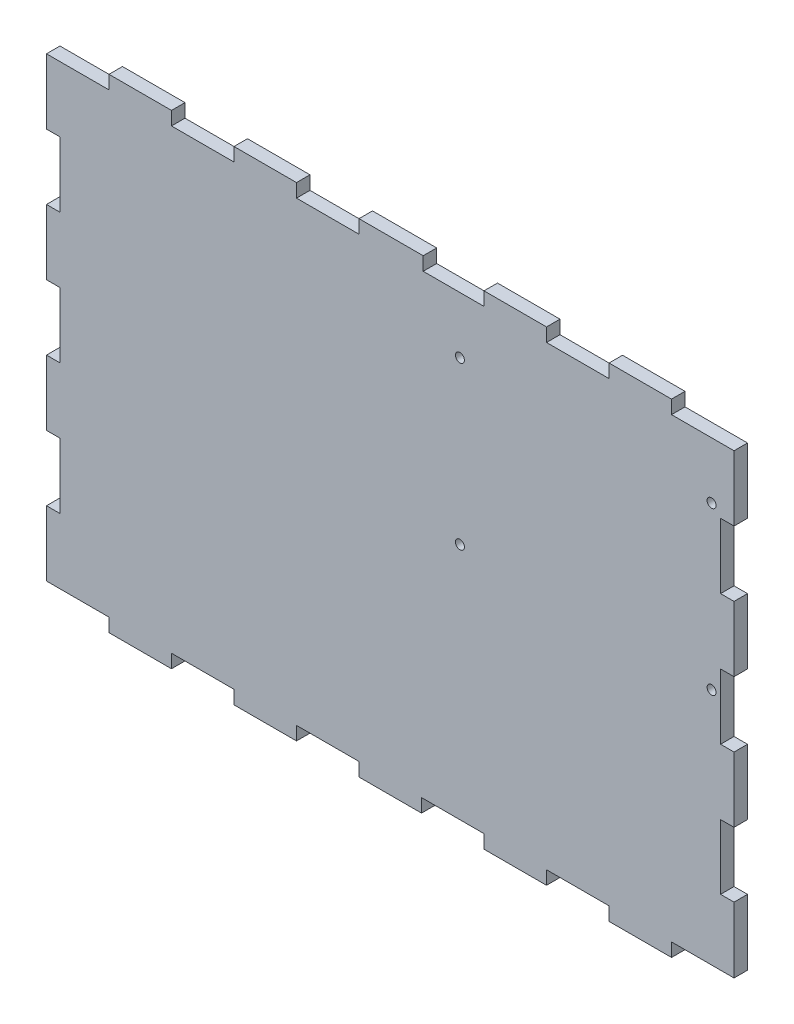
SolidWorks part; units mm, degrees
ref_plane "Alzado" through (0, 0, 0) normal (0, 0, 1) x (1, 0, 0)
ref_plane "Planta" through (0, 0, 0) normal (0, 1, 0) x (1, 0, 0)
ref_plane "Vista lateral" through (0, 0, 0) normal (1, 0, 0) x (0, 0, -1)
sketch "Croquis1" plane through (0, 0, 0) normal (0, 0, 1) x (1, 0, 0)
  line L0 (0, -17.0016) -> (0, -14.0016)
  line L1 (-48.0137, -14.0016) -> (0.3763, -14.0016) construction
  line L2 (0, -17.0016) -> (104.61, -17.0016)
  line L3 (101.61, -17.0016) -> (101.61, -49.332) construction
  line L4 (-227.5797, -78.0016) -> (94.1343, -78.0016) construction
  line L5 (-48.39, -14.0016) -> (-48.39, -78.0016) construction
  line L6 (78.6222, -39.0016) -> (-38.712, -39.0016) construction
  line L7 (0, -14.0016) -> (0, -17.0016) construction
  line L8 (0.3763, -17.0016) -> (-48.0137, -17.0016) construction
  line L9 (-48.39, -14.0016) -> (-38.712, -14.0016)
  line L10 (-38.712, -14.0016) -> (-38.712, -17.0016)
  line L11 (-38.712, -17.0016) -> (-29.034, -17.0016)
  line L12 (-29.034, -17.0016) -> (-29.034, -14.0016)
  line L13 (-29.034, -14.0016) -> (-19.356, -14.0016)
  line L14 (-19.356, -14.0016) -> (-19.356, -17.0016)
  line L15 (-19.356, -17.0016) -> (-9.678, -17.0016)
  line L16 (-9.678, -17.0016) -> (-9.678, -14.0016)
  line L17 (-9.678, -14.0016) -> (0, -14.0016)
  line L18 (104.61, -17.0016) -> (104.61, -78.0016) construction
  line L19 (104.61, -17.0016) -> (104.61, -29.2016)
  line L20 (104.61, -29.2016) -> (101.61, -29.2016)
  line L21 (101.61, -29.2016) -> (101.61, -41.4016)
  line L22 (101.61, -41.4016) -> (104.61, -41.4016)
  line L23 (104.61, -41.4016) -> (104.61, -53.6016)
  line L24 (104.61, -53.6016) -> (101.61, -53.6016)
  line L25 (101.61, -53.6016) -> (101.61, -65.8016)
  line L26 (101.61, -65.8016) -> (104.61, -65.8016)
  line L27 (104.61, -65.8016) -> (104.61, -78.0016)
  line L28 (-45.39, -56.5563) -> (-45.39, 45.6638) construction
  line L29 (-48.39, -14.0016) -> (-48.39, -26.8016)
  line L30 (-48.39, -26.8016) -> (-45.39, -26.8016)
  line L31 (-45.39, -26.8016) -> (-45.39, -39.6016)
  line L32 (-45.39, -39.6016) -> (-48.39, -39.6016)
  line L33 (-48.39, -39.6016) -> (-48.39, -52.4016)
  line L34 (-48.39, -52.4016) -> (-45.39, -52.4016)
  line L35 (-45.39, -52.4016) -> (-45.39, -65.2016)
  line L36 (-45.39, -65.2016) -> (-48.39, -65.2016)
  line L37 (-48.39, -65.2016) -> (-48.39, -78.0016)
  line L38 (-102.1267, -75.0016) -> (76.3072, -75.0016) construction
  line L39 (-124.0097, -156.1001) -> (179.5642, -156.1001) construction
  line L40 (-48.0137, -153.1001) -> (104.9863, -153.1001) construction
  line L41 (-48.39, -78.0016) -> (-34.4809, -78.0016)
  line L42 (-34.4809, -78.0016) -> (-34.4809, -75.0016)
  line L43 (-34.4809, -75.0016) -> (-20.5718, -75.0016)
  line L44 (-20.5718, -75.0016) -> (-20.5718, -78.0016)
  line L45 (-20.5718, -78.0016) -> (-6.6627, -78.0016)
  line L46 (-6.6627, -78.0016) -> (-6.6627, -75.0016)
  line L47 (-6.6627, -75.0016) -> (7.2464, -75.0016)
  line L48 (7.2464, -75.0016) -> (7.2464, -78.0016)
  line L49 (7.2464, -78.0016) -> (21.1555, -78.0016)
  line L50 (21.1555, -78.0016) -> (21.1555, -75.0016)
  line L51 (21.1555, -75.0016) -> (35.0645, -75.0016)
  line L52 (35.0645, -75.0016) -> (35.0645, -78.0016)
  line L53 (35.0645, -78.0016) -> (48.9736, -78.0016)
  line L54 (48.9736, -78.0016) -> (48.9736, -75.0016)
  line L55 (48.9736, -75.0016) -> (62.8827, -75.0016)
  line L56 (62.8827, -75.0016) -> (62.8827, -78.0016)
  line L57 (62.8827, -78.0016) -> (76.7918, -78.0016)
  line L58 (76.7918, -78.0016) -> (76.7918, -75.0016)
  line L59 (76.7918, -75.0016) -> (90.7009, -75.0016)
  line L60 (90.7009, -75.0016) -> (90.7009, -78.0016)
  line L61 (90.7009, -78.0016) -> (104.61, -78.0016)
  line L62 (-48.39, -153.1001) -> (-48.39, -260.7101) construction
  line L63 (-48.0137, -260.7101) -> (104.9863, -260.7101) construction
  line L64 (104.61, -153.1001) -> (104.61, -260.7101) construction
  line L65 (-68.3871, -257.7101) -> (145.2495, -257.7101) construction
  line L66 (101.61, -78.0016) -> (101.61, -269.1968) construction
  line L67 (-45.39, -153.1001) -> (-45.39, -251.8965) construction
  line L68 (-34.4809, -78.0016) -> (-34.4809, -243.0877) construction
  line L69 (-20.5718, -78.0016) -> (-20.5718, -243.0877) construction
  line L70 (-6.6627, -75.0016) -> (-6.6627, -243.0877) construction
  line L71 (7.2464, -75.0016) -> (7.2464, -243.0877) construction
  line L72 (21.1555, -75.0016) -> (21.1555, -243.0877) construction
  line L73 (35.0645, -75.0016) -> (35.0645, -243.0877) construction
  line L74 (48.9736, -75.0016) -> (48.9736, -243.0877) construction
  line L75 (62.8827, -75.0016) -> (62.8827, -243.0877) construction
  line L76 (76.7918, -75.0016) -> (76.7918, -243.0877) construction
  line L77 (90.7009, -75.0016) -> (90.7009, -243.0877) construction
  line L78 (-34.4809, -156.1001) -> (-48.39, -156.1001)
  line L79 (-34.4809, -156.1001) -> (-34.4809, -153.1001)
  line L80 (-34.4809, -153.1001) -> (-20.5718, -153.1001)
  line L81 (-20.5718, -153.1001) -> (-20.5718, -156.1001)
  line L82 (-20.5718, -156.1001) -> (-6.6627, -156.1001)
  line L83 (-6.6627, -156.1001) -> (-6.6627, -153.1001)
  line L84 (-6.6627, -153.1001) -> (7.2464, -153.1001)
  line L85 (7.2464, -153.1001) -> (7.2464, -156.1001)
  line L86 (7.2464, -156.1001) -> (21.1555, -156.1001)
  line L87 (21.1555, -156.1001) -> (21.1555, -153.1001)
  line L88 (21.1555, -153.1001) -> (35.4409, -153.1001)
  line L89 (35.4409, -153.1001) -> (35.4409, -156.1001)
  line L90 (35.4409, -156.1001) -> (48.9736, -156.1001)
  line L91 (48.9736, -156.1001) -> (48.9736, -153.1001)
  line L92 (48.9736, -153.1001) -> (62.8827, -153.1001)
  line L93 (62.8827, -153.1001) -> (62.8827, -156.1001)
  line L94 (62.8827, -156.1001) -> (76.7918, -156.1001)
  line L95 (76.7918, -156.1001) -> (76.7918, -153.1001)
  line L96 (76.7918, -153.1001) -> (90.7009, -153.1001)
  line L97 (90.7009, -153.1001) -> (90.7009, -156.1001)
  line L98 (90.7009, -156.1001) -> (104.61, -156.1001)
  line L99 (-48.39, -257.7101) -> (-34.4809, -257.7101)
  line L100 (-34.4809, -257.7101) -> (-34.4809, -260.7101)
  line L101 (-34.4809, -260.7101) -> (-20.5718, -260.7101)
  line L102 (-20.5718, -260.7101) -> (-20.5718, -257.7101)
  line L103 (-20.5718, -257.7101) -> (-6.6627, -257.7101)
  line L104 (-6.6627, -257.7101) -> (-6.6627, -260.7101)
  line L105 (-6.6627, -260.7101) -> (7.2464, -260.7101)
  line L106 (7.2464, -260.7101) -> (7.2464, -257.7101)
  line L107 (7.2464, -257.7101) -> (21.1555, -257.7101)
  line L108 (21.1555, -257.7101) -> (21.1555, -260.7101)
  line L109 (21.1555, -260.7101) -> (35.0645, -260.7101)
  line L110 (35.0645, -260.7101) -> (35.0645, -257.7101)
  line L111 (35.0645, -257.7101) -> (48.9736, -257.7101)
  line L112 (48.9736, -257.7101) -> (48.9736, -260.7101)
  line L113 (48.9736, -260.7101) -> (62.8827, -260.7101)
  line L114 (62.8827, -260.7101) -> (62.8827, -257.7101)
  line L115 (62.8827, -257.7101) -> (76.7918, -257.7101)
  line L116 (76.7918, -257.7101) -> (76.7918, -260.7101)
  line L117 (76.7918, -260.7101) -> (90.7009, -260.7101)
  line L118 (90.7009, -260.7101) -> (90.7009, -257.7101)
  line L119 (90.7009, -257.7101) -> (104.61, -257.7101)
  line L120 (-225.8763, -14.0016) -> (-225.8763, -78.0016) construction
  line L121 (-289.8763, -78.0016) -> (-225.8763, -78.0016) construction
  line L122 (-225.8763, -78.0016) -> (-225.8763, -287.7111) construction
  line L123 (-289.8763, -78.0016) -> (-289.8763, -287.7111) construction
  line L124 (-289.8763, -287.7111) -> (-225.8763, -287.7111) construction
  line L125 (-48.0137, -26.8016) -> (-105.1743, -26.8016) construction
  line L126 (-48.0137, -39.6016) -> (-94.3752, -39.6016) construction
  line L127 (-48.0137, -52.4016) -> (-71.4298, -52.4016) construction
  line L128 (-48.0137, -65.2016) -> (-67.3697, -65.2016) construction
  line L129 (-277.0763, -73.8444) -> (-277.0763, -111.8004) construction
  line L130 (-264.2763, -73.8444) -> (-264.2763, -111.8004) construction
  line L131 (-251.4763, -90.832) -> (-251.4763, -128.788) construction
  line L132 (-238.6763, -73.8444) -> (-238.6763, -111.8004) construction
  line L133 (-228.8763, -73.8444) -> (-228.8763, -93.389) construction
  line L134 (165.7334, -156.1001) -> (174.9334, -156.1001)
  line L135 (174.9334, -156.1001) -> (174.9334, -153.1001)
  line L136 (174.9334, -153.1001) -> (187.1334, -153.1001)
  line L137 (187.1334, -153.1001) -> (187.1334, -156.1001)
  line L138 (187.1334, -156.1001) -> (199.3334, -156.1001)
  line L139 (199.3334, -156.1001) -> (199.3334, -153.1001)
  line L140 (199.3334, -153.1001) -> (211.5334, -153.1001)
  line L141 (211.5334, -153.1001) -> (211.5334, -156.1001)
  line L142 (211.5334, -156.1001) -> (223.7334, -156.1001)
  line L143 (-228.8763, -156.1001) -> (-228.8763, -170.6158)
  line L144 (-228.8763, -170.6158) -> (-225.8763, -170.6158)
  line L145 (-225.8763, -170.6158) -> (-225.8763, -185.1315)
  line L146 (-225.8763, -185.1315) -> (-228.8763, -185.1315)
  line L147 (-228.8763, -185.1315) -> (-228.8763, -199.6473)
  line L148 (-228.8763, -199.6473) -> (-225.8763, -199.6473)
  line L149 (-225.8763, -199.6473) -> (-225.8763, -220.163)
  line L150 (-225.8763, -220.163) -> (-228.8763, -220.163)
  line L151 (-48.39, -257.7101) -> (-48.39, -243.1944)
  line L152 (-48.39, -243.1944) -> (-45.39, -243.1944)
  line L153 (-45.39, -243.1944) -> (-45.39, -228.6787)
  line L154 (-45.39, -228.6787) -> (-48.39, -228.6787)
  line L155 (-48.39, -228.6787) -> (-48.39, -214.163)
  line L156 (-48.39, -214.163) -> (-45.39, -214.163)
  line L157 (-45.39, -214.163) -> (-45.39, -199.6473)
  line L158 (-45.39, -199.6473) -> (-48.39, -199.6473)
  line L159 (-48.39, -199.6473) -> (-48.39, -185.1315)
  line L160 (-48.39, -185.1315) -> (-45.39, -185.1315)
  line L161 (-45.39, -185.1315) -> (-45.39, -170.6158)
  line L162 (-45.39, -170.6158) -> (-48.39, -170.6158)
  line L163 (-48.39, -170.6158) -> (-48.39, -156.1001)
  line L164 (-48.0137, -228.6787) -> (-80.0216, -228.6787) construction
  line L165 (-48.0137, -243.1944) -> (-76.5227, -243.1944) construction
  line L166 (-48.0137, -214.163) -> (-74.4233, -214.163) construction
  line L167 (-48.0137, -199.6473) -> (-74.4233, -199.6473) construction
  line L168 (-74.4233, -185.1315) -> (-48.0137, -185.1315) construction
  line L169 (-48.0137, -170.6158) -> (-70.6911, -170.6158) construction
  line L170 (-228.8763, -220.163) -> (-228.8763, -234.6787)
  line L171 (-286.8763, -73.8444) -> (-286.8763, -109.848) construction
  line L172 (-228.8763, -234.6787) -> (-225.8763, -234.6787)
  line L173 (-225.8763, -234.6787) -> (-225.8763, -249.1944)
  line L174 (-225.8763, -249.1944) -> (-228.8763, -249.1944)
  line L175 (-228.8763, -249.1944) -> (-228.8763, -257.7101)
  line L176 (223.7334, -257.7101) -> (211.5334, -257.7101)
  line L177 (211.5334, -257.7101) -> (211.5334, -260.7101)
  line L178 (211.5334, -260.7101) -> (199.3334, -260.7101)
  line L179 (199.3334, -260.7101) -> (199.3334, -257.7101)
  line L180 (199.3334, -257.7101) -> (187.1334, -257.7101)
  line L181 (187.1334, -257.7101) -> (187.1334, -260.7101)
  line L182 (187.1334, -260.7101) -> (174.9334, -260.7101)
  line L183 (174.9334, -260.7101) -> (174.9334, -257.7101)
  line L184 (-286.8763, -257.7101) -> (-286.8763, -243.1944)
  line L185 (-286.8763, -243.1944) -> (-289.8763, -243.1944)
  line L186 (-289.8763, -243.1944) -> (-289.8763, -228.6787)
  line L187 (-289.8763, -228.6787) -> (-286.8763, -228.6787)
  line L188 (-286.8763, -228.6787) -> (-286.8763, -214.163)
  line L189 (-286.8763, -214.163) -> (-289.8763, -214.163)
  line L190 (-289.8763, -214.163) -> (-289.8763, -199.6473)
  line L191 (-289.8763, -199.6473) -> (-286.8763, -199.6473)
  line L192 (-286.8763, -199.6473) -> (-286.8763, -185.1315)
  line L193 (-286.8763, -185.1315) -> (-289.8763, -185.1315)
  line L194 (-289.8763, -185.1315) -> (-289.8763, -170.6158)
  line L195 (-289.8763, -170.6158) -> (-286.8763, -170.6158)
  line L196 (-286.8763, -170.6158) -> (-286.8763, -156.1001)
  line L197 (174.9334, -257.7101) -> (165.7334, -257.7101)
  line L198 (-315.1106, -120.5373) -> (-315.1106, -274.6014) construction
  line L199 (-422.7206, -153.1001) -> (-422.7206, -80.2802) construction
  line L200 (-419.7206, -153.1001) -> (-419.7206, -73.0846) construction
  line L201 (-405.2049, -153.1001) -> (-405.2049, -73.0846) construction
  line L202 (-390.6892, -153.1001) -> (-390.6892, -77.6291) construction
  line L203 (-376.1735, -153.1001) -> (-376.1735, -80.2802) construction
  line L204 (-361.6578, -153.1001) -> (-361.6578, -73.0846) construction
  line L205 (-347.1421, -153.1001) -> (-347.1421, -77.6291) construction
  line L206 (-332.6263, -153.1001) -> (-332.6263, -73.0846) construction
  line L207 (-318.1106, -153.1001) -> (-318.1106, -77.6291) construction
  line L208 (-48.39, -21.6772) -> (-48.39, 38.9813) construction
  line L209 (-38.712, -14.0016) -> (-38.712, 45.6638) construction
  line L210 (-29.034, -14.0016) -> (-29.034, 45.6638) construction
  line L211 (-19.356, -14.0016) -> (-19.356, 45.6638) construction
  line L212 (-9.678, -14.0016) -> (-9.678, 45.6638) construction
  line L213 (0, -14.0016) -> (0, 45.6638) construction
  line L214 (2.8912, 38.1832) -> (-48.39, 38.1832) construction
  line L215 (-48.0137, 86.5732) -> (-79.7385, 86.5732) construction
  line L216 (-48.39, 76.8952) -> (-75.2531, 76.8952) construction
  line L217 (-48.39, 67.2172) -> (-75.2531, 67.2172) construction
  line L218 (-48.39, 57.5392) -> (-80.1148, 57.5392) construction
  line L219 (-48.39, 47.8612) -> (-84.9766, 47.8612) construction
  line L220 (-318.1106, 38.1832) -> (-318.1106, 47.8612)
  line L221 (-48.0137, 38.1832) -> (-76.5678, 38.1832) construction
  line L222 (-318.1106, 47.8612) -> (-315.1106, 47.8612)
  line L223 (-315.1106, 47.8612) -> (-315.1106, 57.5392)
  line L224 (-315.1106, 57.5392) -> (-318.1106, 57.5392)
  line L225 (-318.1106, 57.5392) -> (-318.1106, 67.2172)
  line L226 (-318.1106, 67.2172) -> (-315.1106, 67.2172)
  line L227 (-315.1106, 67.2172) -> (-315.1106, 76.8952)
  line L228 (-315.1106, 76.8952) -> (-318.1106, 76.8952)
  line L229 (-318.1106, 76.8952) -> (-318.1106, 86.5732)
  line L230 (-318.1106, 86.5732) -> (-419.7206, 86.5732)
  line L231 (-419.7206, 86.5732) -> (-419.7206, 76.8952)
  line L232 (-419.7206, 76.8952) -> (-422.7206, 76.8952)
  line L233 (-422.7206, 76.8952) -> (-422.7206, 67.2172)
  line L234 (-422.7206, 67.2172) -> (-419.7206, 67.2172)
  line L235 (-419.7206, 67.2172) -> (-419.7206, 57.5392)
  line L236 (-419.7206, 57.5392) -> (-422.7206, 57.5392)
  line L237 (-422.7206, 57.5392) -> (-422.7206, 47.8612)
  line L238 (-422.7206, 47.8612) -> (-419.7206, 47.8612)
  line L239 (-419.7206, 47.8612) -> (-419.7206, 38.1832)
  line L240 (-48.0137, 41.1832) -> (-83.5753, 41.1832) construction
  line L241 (-318.1106, 38.1832) -> (-332.6263, 38.1832)
  line L242 (-332.6263, 38.1832) -> (-332.6263, 41.1832)
  line L243 (-332.6263, 41.1832) -> (-347.1421, 41.1832)
  line L244 (-347.1421, 41.1832) -> (-347.1421, 38.1832)
  line L245 (-347.1421, 38.1832) -> (-361.6578, 38.1832)
  line L246 (-361.6578, 38.1832) -> (-361.6578, 41.1832)
  line L247 (-361.6578, 41.1832) -> (-376.1735, 41.1832)
  line L248 (-376.1735, 41.1832) -> (-376.1735, 38.1832)
  line L249 (-376.1735, 38.1832) -> (-390.6892, 38.1832)
  line L250 (-390.6892, 38.1832) -> (-390.6892, 41.1832)
  line L251 (-390.6892, 41.1832) -> (-405.2049, 41.1832)
  line L252 (-405.2049, 41.1832) -> (-405.2049, 38.1832)
  line L253 (-405.2049, 38.1832) -> (-419.7206, 38.1832)
  line L254 (162.7334, -15.1529) -> (162.7334, -104.9762) construction
  line L255 (104.9863, -29.2016) -> (146.268, -29.2016) construction
  line L256 (104.9863, -41.4016) -> (146.268, -41.4016) construction
  line L257 (104.9863, -65.8016) -> (131.818, -65.8016) construction
  line L258 (104.9863, -53.6016) -> (126.9205, -53.6016) construction
  line L259 (165.7334, -73.8444) -> (165.7334, -106.8492) construction
  line L260 (174.9334, -73.8444) -> (174.9334, -108.8044) construction
  line L261 (187.1334, -73.8444) -> (187.1334, -108.8044) construction
  line L262 (199.3334, -73.8444) -> (199.3334, -108.8044) construction
  line L263 (211.5334, -73.8444) -> (211.5334, -106.8492) construction
  line L264 (223.7334, -73.8444) -> (223.7334, -108.8044) construction
  line L265 (104.61, -257.7101) -> (104.61, -243.0877)
  line L266 (104.61, -243.0877) -> (101.61, -243.0877)
  line L267 (101.61, -243.0877) -> (101.61, -228.6787)
  line L268 (101.61, -228.6787) -> (104.61, -228.6787)
  line L269 (104.61, -228.6787) -> (104.61, -214.163)
  line L270 (104.61, -214.163) -> (101.61, -214.163)
  line L271 (101.61, -214.163) -> (101.61, -199.6473)
  line L272 (101.61, -199.6473) -> (104.61, -199.6473)
  line L273 (104.61, -199.6473) -> (104.61, -185.1315)
  line L274 (104.61, -185.1315) -> (101.61, -185.1315)
  line L275 (101.61, -185.1315) -> (101.61, -170.6158)
  line L276 (101.61, -170.6158) -> (104.61, -170.6158)
  line L277 (104.61, -170.6158) -> (104.61, -156.1001)
  line L278 (-228.8763, -156.1001) -> (-238.6763, -156.1001)
  line L279 (-238.6763, -156.1001) -> (-238.6763, -153.1001)
  line L280 (-238.6763, -153.1001) -> (-251.4763, -153.1001)
  line L281 (-251.4763, -153.1001) -> (-251.4763, -156.1001)
  line L282 (-251.4763, -156.1001) -> (-264.2763, -156.1001)
  line L283 (-264.2763, -156.1001) -> (-264.2763, -153.1001)
  line L284 (-264.2763, -153.1001) -> (-277.0763, -153.1001)
  line L285 (-277.0763, -153.1001) -> (-277.0763, -156.1001)
  line L286 (-277.0763, -156.1001) -> (-286.8763, -156.1001)
  line L287 (223.7334, -156.1001) -> (223.7334, -257.7101)
  line L288 (-228.8763, -257.7101) -> (-238.6763, -257.7101)
  line L289 (-238.6763, -257.7101) -> (-238.6763, -260.7101)
  line L290 (-238.6763, -260.7101) -> (-251.4763, -260.7101)
  line L291 (-251.4763, -260.7101) -> (-251.4763, -257.7101)
  line L292 (-251.4763, -257.7101) -> (-264.2763, -257.7101)
  line L293 (-264.2763, -257.7101) -> (-264.2763, -260.7101)
  line L294 (-264.2763, -260.7101) -> (-277.0763, -260.7101)
  line L295 (-277.0763, -260.7101) -> (-277.0763, -257.7101)
  line L296 (-277.0763, -257.7101) -> (-286.8763, -257.7101)
  line L297 (165.7334, -257.7101) -> (165.7334, -243.1944)
  line L298 (165.7334, -243.1944) -> (162.7334, -243.1944)
  line L299 (162.7334, -243.1944) -> (162.7334, -228.6787)
  line L300 (162.7334, -228.6787) -> (165.7334, -228.6787)
  line L301 (165.7334, -228.6787) -> (165.7334, -214.163)
  line L302 (165.7334, -214.163) -> (162.7334, -214.163)
  line L303 (162.7334, -214.163) -> (162.7334, -199.6473)
  line L304 (162.7334, -199.6473) -> (165.7334, -199.6473)
  line L305 (165.7334, -199.6473) -> (165.7334, -185.1315)
  line L306 (165.7334, -185.1315) -> (162.7334, -185.1315)
  line L307 (162.7334, -185.1315) -> (162.7334, -170.6158)
  line L308 (162.7334, -170.6158) -> (165.7334, -170.6158)
  line L309 (165.7334, -170.6158) -> (165.7334, -156.1001)
  line L310 (101.61, -186.6701) -> (41.61, -186.6701) construction
  line L311 (101.61, -166.6701) -> (41.61, -166.6701) construction
  line L312 (101.61, -166.6701) -> (101.61, -206.6701) construction
  line L313 (101.61, -206.6701) -> (41.61, -206.6701) construction
  line L314 (41.61, -166.6701) -> (41.61, -206.6701) construction
  line L315 (71.61, -166.6701) -> (71.61, -206.6701) construction
  circle A0 centre (73.11, -39.0016) radius 1.25
  circle A1 centre (31.5, -39.0016) radius 1.25
  circle A2 centre (-28.49, -39.0016) radius 1.25
  arc A3 (-225.8763, -65.2016) -> (-238.6763, -78.0016) centre (-225.8763, -78.0016) ccw construction
  arc A4 (-225.8763, -52.4016) -> (-251.4763, -78.0016) centre (-225.8763, -78.0016) ccw construction
  arc A5 (-225.8763, -39.6016) -> (-264.2763, -78.0016) centre (-225.8763, -78.0016) ccw construction
  arc A6 (-225.8763, -26.8016) -> (-277.0763, -78.0016) centre (-225.8763, -78.0016) ccw construction
  arc A7 (-225.8763, -14.0016) -> (-289.8763, -78.0016) centre (-225.8763, -78.0016) ccw construction
  arc A8 (-225.8763, -75.0016) -> (-228.8763, -78.0016) centre (-225.8763, -78.0016) ccw construction
  arc A9 (-225.8763, -17.0016) -> (-286.8763, -78.0016) centre (-225.8763, -78.0016) ccw construction
  arc A10 (-315.1106, -156.1001) -> (-318.1106, -153.1001) centre (-315.1106, -153.1001) cw construction
  arc A11 (-315.1106, -170.6158) -> (-332.6263, -153.1001) centre (-315.1106, -153.1001) cw construction
  arc A12 (-315.1106, -185.1315) -> (-347.1421, -153.1001) centre (-315.1106, -153.1001) cw construction
  arc A13 (-315.1106, -199.6473) -> (-361.6578, -153.1001) centre (-315.1106, -153.1001) cw construction
  arc A14 (-315.1106, -214.163) -> (-376.1735, -153.1001) centre (-315.1106, -153.1001) cw construction
  arc A15 (-315.1106, -228.6787) -> (-390.6892, -153.1001) centre (-315.1106, -153.1001) cw construction
  arc A16 (-315.1106, -243.1944) -> (-405.2049, -153.1001) centre (-315.1106, -153.1001) cw construction
  arc A17 (-315.1106, -257.7101) -> (-419.7206, -153.1001) centre (-315.1106, -153.1001) cw construction
  arc A18 (-315.1106, -260.7101) -> (-422.7206, -153.1001) centre (-315.1106, -153.1001) cw construction
  arc A19 (-45.39, 38.1832) -> (-48.39, 41.1832) centre (-48.39, 38.1832) ccw construction
  arc A20 (-38.712, 38.1832) -> (-48.39, 47.8612) centre (-48.39, 38.1832) ccw construction
  arc A21 (-29.034, 38.1832) -> (-48.39, 57.5392) centre (-48.39, 38.1832) ccw construction
  arc A22 (-19.356, 38.1832) -> (-48.39, 67.2172) centre (-48.39, 38.1832) ccw construction
  arc A23 (-9.678, 38.1832) -> (-48.39, 76.8952) centre (-48.39, 38.1832) ccw construction
  arc A24 (0, 38.1832) -> (-48.39, 86.5732) centre (-48.39, 38.1832) ccw construction
  arc A25 (162.7334, -75.0016) -> (165.7334, -78.0016) centre (162.7334, -78.0016) cw construction
  arc A26 (162.7334, -65.8016) -> (174.9334, -78.0016) centre (162.7334, -78.0016) cw construction
  arc A27 (162.7334, -53.6016) -> (187.1334, -78.0016) centre (162.7334, -78.0016) cw construction
  arc A28 (162.7334, -41.4016) -> (199.3334, -78.0016) centre (162.7334, -78.0016) cw construction
  arc A29 (162.7334, -29.2016) -> (211.5334, -78.0016) centre (162.7334, -78.0016) cw construction
  arc A30 (162.7334, -17.0016) -> (223.7334, -78.0016) centre (162.7334, -78.0016) cw construction
  circle A31 centre (99.61, -168.6701) radius 1
  circle A32 centre (99.61, -204.6701) radius 1
  circle A33 centre (43.61, -168.6701) radius 1
  circle A34 centre (43.61, -204.6701) radius 1
  text T0 "TOP\r\n"
  dimension "D2" = 2.5
  dimension "D3" = 2.5
  dimension "D4" = 2.5
  dimension "D7" = 101.6
  dimension "D20" = 22
  dimension "D9" = 36
  dimension "D21" = 2
  dimension "D22" = 2
  dimension "D1" = 153
  dimension "D5" = 3
  dimension "D6" = 104.61
  dimension "D8" = 3
  dimension "D10" = 3
  dimension "D11" = 41.61
  dimension "D12" = 40
  dimension "D13" = 3
  dimension "D14" = 153
  dimension "D15" = 107.61
  dimension "D16" = 60
  dimension "D17" = 3
  dimension "D18" = 3
  dimension "D19" = 28.5
  dimension "D23" = 2
  dimension "D24" = 51.04
extrude "Saliente-Extruir1" add sketch "Croquis1" along normal blind 3 contours L276 L277 L98 L97 L96 L95 L94 L93 L92 L91 L90 L89 L88 L87 L86 L85 L84 L83 L82 L81 L80 L79 L78 L163 L162 L161 L160 L159 L158 L157 L156 L155 L154 L153 L152 L151 L99 L100 L101 L102 L103 L104 L105 L106 L107 L108 L109 L110 L111 L112 L113
